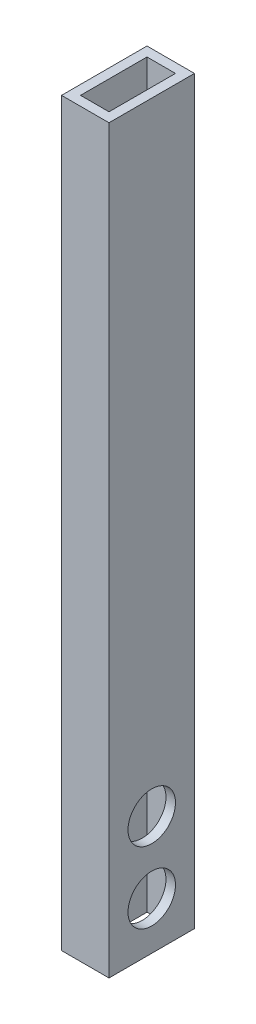
SolidWorks part; units mm, degrees
ref_plane "Front Plane" through (0, 0, 0) normal (0, 0, 1) x (1, 0, 0)
ref_plane "Top Plane" through (0, 0, 0) normal (0, 1, 0) x (1, 0, 0)
ref_plane "Right Plane" through (0, 0, 0) normal (1, 0, 0) x (0, 0, -1)
sketch "Sketch1" plane through (0, 0, 0) normal (0, 0, 1) x (1, 0, 0)
  line L1 (-5, 125) -> (5, 125)
  line L2 (-5, 125) -> (-5, -125)
  line L3 (-5, -125) -> (5, -125)
  line L4 (5, 125) -> (5, -125)
  line L5 (-5, 125) -> (5, -125) construction
  line L6 (-5, -125) -> (5, 125) construction
  point P0 (0, 0)
  dimension "D1" = 10
  dimension "D2" = 250
extrude "Boss-Extrude1" add sketch "Sketch1" along normal blind 18
shell "Shell1" thickness 2
sketch "Sketch3" plane through (-5, 0, 0) normal (-1, 0, 0) x (0, 0, 1)
  circle A1 centre (9, -100) radius 5
  dimension "D1" = 10
extrude "Cut-Extrude2" cut sketch "Sketch3" against normal blind 10
sketch "Sketch4" plane through (5, 0, 0) normal (1, 0, 0) x (0, 0, -1)
  line L0 (0, 125) -> (0, -125) construction
  line L1 (-16, -125) -> (-2, -125) construction
  circle A0 centre (-9, -115) radius 5
  dimension "D1" = 10
  dimension "D2" = 9
  dimension "D3" = 10
extrude "Cut-Extrude3" cut sketch "Sketch4" against normal blind 10
sketch "Sketch5" plane through (5, 0, 0) normal (1, 0, 0) x (0, 0, -1)
  line L0 (0, 125) -> (0, -125) construction
  line L1 (-18, 125) -> (0, 125)
  line L2 (-18, 125) -> (-18, 31)
  line L3 (-18, 31) -> (0, 31)
  line L4 (0, 125) -> (0, 31)
  dimension "D1" = 94
extrude "Cut-Extrude4" cut sketch "Sketch5" against normal blind 10
